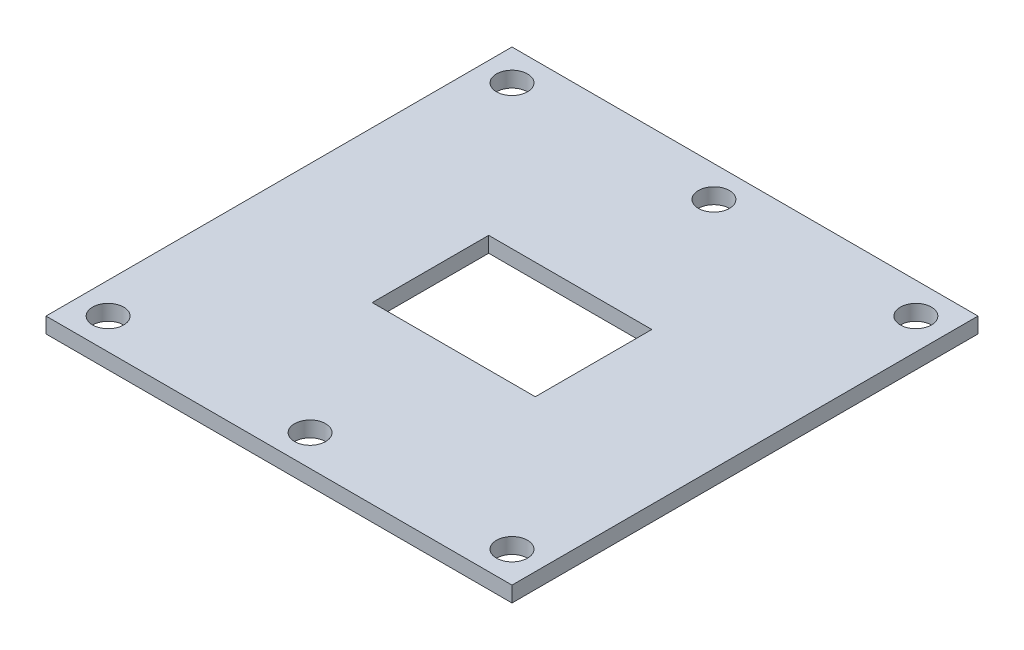
SolidWorks part; units mm, degrees
ref_plane "Front Plane" through (0, 0, 0) normal (0, 0, 1) x (1, 0, 0)
ref_plane "Top Plane" through (0, 0, 0) normal (0, 1, 0) x (1, 0, 0)
ref_plane "Right Plane" through (0, 0, 0) normal (1, 0, 0) x (0, 0, -1)
sketch "Sketch1" plane through (0, 0, 0) normal (0, 1, 0) x (1, 0, 0)
  line L1 (30, -30) -> (-30, -30)
  line L2 (30, -30) -> (30, 30)
  line L3 (30, 30) -> (-30, 30)
  line L4 (-30, -30) -> (-30, 30)
  line L5 (30, -30) -> (-30, 30) construction
  line L6 (30, 30) -> (-30, -30) construction
  point P0 (0, 0)
  dimension "D1" = 60
  dimension "D2" = 60
extrude "Boss-Extrude1" add sketch "Sketch1" along normal blind 2
sketch "Sketch2" plane through (0, 2, 0) normal (0, 1, 0) x (1, 0, 0)
  line L0 (30, 30) -> (-30, 30) construction
  line L2 (-30, 30) -> (-30, -30) construction
  line L3 (30, -30) -> (30, 30) construction
  line L5 (-30, -30) -> (30, -30) construction
  line L7 (-30, 30) -> (-30, -30) construction
  circle A0 centre (-26, 26) radius 2
  circle A1 centre (0, 26) radius 2
  circle A2 centre (26, 26) radius 2
  circle A3 centre (26, -26) radius 2
  circle A4 centre (0, -26) radius 2
  circle A5 centre (-26, -26) radius 2
  dimension "D1" = 4
  dimension "D5" = 4
  dimension "D7" = 4
  dimension "D10" = 4
  dimension "D16" = 4
  dimension "D17" = 4
  dimension "D2" = 4
  dimension "D3" = 4
  dimension "D4" = 4
  dimension "D6" = 0
  dimension "D8" = 4
  dimension "D9" = 4
  dimension "D11" = 4
  dimension "D12" = 4
  dimension "D13" = 4
  dimension "D14" = 4
  dimension "D15" = 4
  dimension "D18" = 0
extrude "Cut-Extrude1" cut sketch "Sketch2" against normal through all
sketch "Sketch3" plane through (0, 2, 0) normal (0, 1, 0) x (1, 0, 0)
  line L1 (10.5, -7.5) -> (-10.5, -7.5)
  line L2 (10.5, -7.5) -> (10.5, 7.5)
  line L3 (10.5, 7.5) -> (-10.5, 7.5)
  line L4 (-10.5, -7.5) -> (-10.5, 7.5)
  line L5 (10.5, -7.5) -> (-10.5, 7.5) construction
  line L6 (10.5, 7.5) -> (-10.5, -7.5) construction
  point P0 (0, 0)
  dimension "D1" = 21
  dimension "D2" = 15
extrude "Cut-Extrude2" cut sketch "Sketch3" against normal blind 2
